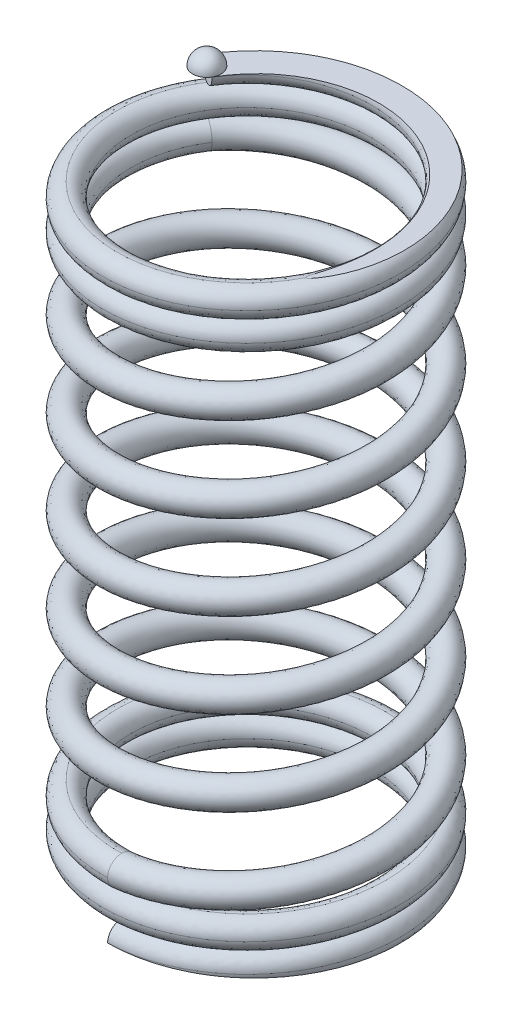
SolidWorks part; units mm, degrees
ref_plane "Front Plane" through (0, 0, 0) normal (0, 0, 1) x (1, 0, 0)
ref_plane "Top Plane" through (0, 0, 0) normal (0, 1, 0) x (1, 0, 0)
ref_plane "Right Plane" through (0, 0, 0) normal (1, 0, 0) x (0, 0, -1)
sketch "Sketch3" plane through (0, 0, 0) normal (0, 1, 0) x (1, 0, 0)
  circle A0 centre (0, 0) radius 4.75
  dimension "D1" = 9.5
ref_plane "Plane1" through (0, 2, 0) normal (0, 1, 0) x (1, 0, 0)
sketch "Sketch4" plane through (0, 0, 0) normal (0, 1, 0) x (1, 0, 0)
  circle A0 centre (0, 0) radius 4.75
  dimension "D1" = 9.5
curve "Helix/Spiral3" pitch 1 height 2 turns 2
sketch "Sketch5" plane through (0, 2, 0) normal (0, 1, 0) x (1, 0, 0)
  circle A0 centre (0, 0) radius 4.75
  dimension "D1" = 9.5
sketch "Sketch7" plane through (0, 0, 0) normal (1, 0, 0) x (0, 0, -1)
  line L0 (5.6185, 0) -> (-5.6185, 0) construction
  circle A0 centre (-4.75, 0) radius 0.5
  dimension "D2" = 1
  dimension "D1" = 4.75
sweep "Sweep5" add profiles "Sketch7" path "Helix/Spiral3"
sketch "Sketch13" plane through (0, 2, 0) normal (0, 1, 0) x (1, 0, 0)
  circle A0 centre (0, 0) radius 4.75
  dimension "D1" = 9.5
curve "Helix/Spiral6" pitch 3 height 17 turns 5.6667
sketch "Sketch15" plane through (0, 0, 0) normal (1, 0, 0) x (0, 0, -1)
  line L0 (5.6185, 2) -> (-5.6185, 2) construction
  circle A0 centre (-4.75, 2) radius 0.5
  spline S0 degree 3 poles (-4.75, 2) (-4.75, 2.0626) (-4.499, 2.1891) (-3.4274, 2.3777) (-1.8264, 2.5667) (0.0567, 2.7556) (1.9311, 2.9444) (3.5072, 3.1333) (4.5415, 3.3222) (4.8742, 3.5111) (4.454, 3.7) (3.3458, 3.8889) (1.7207, 4.0778) (-0.1702, 4.2667) (-2.0347, 4.4556) (-3.585, 4.6444) (-4.5815, 4.8333) (-4.8702, 5.0222) (-4.4067, 5.2111) (-3.2624, 5.4) (-1.6141, 5.5889) (0.2835, 5.7778) (2.1373, 5.9667) (3.6609, 6.1556) (4.6191, 6.3444) (4.8636, 6.5333) (4.3569, 6.7222) (3.1772, 6.9111) (1.5066, 7.1) (-0.3967, 7.2889) (-2.2387, 7.4778) (-3.7349, 7.6667) (-4.6541, 7.8556) (-4.8544, 8.0444) (-4.3048, 8.2333) (-3.0903, 8.4222) (-1.3983, 8.6111) (0.5096, 8.8) (2.3389, 8.9889) (3.8068, 9.1778) (4.6867, 9.3667) (4.8426, 9.5556) (4.2504, 9.7444) (3.0017, 9.9333) (1.2893, 10.1222) (-0.6223, 10.3111) (-2.4378, 10.5) (-3.8766, 10.6889) (-4.7167, 10.8778) (-4.8281, 11.0667) (-4.1937, 11.2556) (-2.9115, 11.4444) (-1.1795, 11.6333) (0.7347, 11.8222) (2.5354, 12.0111) (3.9444, 12.2) (4.7441, 12.3889) (4.811, 12.5778) (4.1347, 12.7667) (2.8197, 12.9556) (1.0691, 13.1444) (-0.8466, 13.3333) (-2.6316, 13.5222) (-4.01, 13.7111) (-4.769, 13.9) (-4.7913, 14.0889) (-4.0734, 14.2778) (-2.7264, 14.4667) (-0.9581, 14.6556) (0.9581, 14.8444) (2.7264, 15.0333) (4.0734, 15.2222) (4.7913, 15.4111) (4.769, 15.6) (4.01, 15.7889) (2.6316, 15.9778) (0.8466, 16.1667) (-1.0691, 16.3556) (-2.8197, 16.5444) (-4.1347, 16.7333) (-4.811, 16.9222) (-4.7441, 17.1111) (-3.9444, 17.3) (-2.5354, 17.4889) (-0.7347, 17.6778) (1.1795, 17.8667) (2.9115, 18.0556) (4.1936, 18.2444) (4.8282, 18.4333) (4.7162, 18.6223) (3.8782, 18.8109) (2.914, 18.9374) (2.375, 19) knots 0 0 0 0 0.011111 0.022222 0.033333 0.044444 0.055556 0.066667 0.077778 0.088889 0.1 0.111111 0.122222 0.133333 0.144444 0.155556 0.166667 0.177778 0.188889 0.2 0.211111 0.222222 0.233333 0.244444 0.255556 0.266667 0.277778 0.288889 0.3 0.311111 0.322222 0.333333 0.344444 0.355556 0.366667 0.377778 0.388889 0.4 0.411111 0.422222 0.433333 0.444444 0.455556 0.466667 0.477778 0.488889 0.5 0.511111 0.522222 0.533333 0.544444 0.555556 0.566667 0.577778 0.588889 0.6 0.611111 0.622222 0.633333 0.644444 0.655556 0.666667 0.677778 0.688889 0.7 0.711111 0.722222 0.733333 0.744444 0.755556 0.766667 0.777778 0.788889 0.8 0.811111 0.822222 0.833333 0.844444 0.855556 0.866667 0.877778 0.888889 0.9 0.911111 0.922222 0.933333 0.944444 0.955556 0.966667 0.977778 0.988889 1 1 1 1 construction
sweep "Sweep6" add profiles "Sketch15" path "Helix/Spiral6"
ref_plane "Plane4" through (0, 19, 0) normal (0, 1, 0) x (1, 0, 0)
sketch "Sketch16" plane through (0, 19, 0) normal (0, 1, 0) x (1, 0, 0)
  circle A0 centre (0, 0) radius 4.75
  dimension "D1" = 9.5
curve "Helix/Spiral7" pitch 1 height 2 turns 2
sketch "Sketch18" plane through (0, 0, 0) normal (-1, 0, 0) x (0, 0, 1)
  line L0 (5.6185, 0) -> (-5.6185, 0) construction
  line L1 (6.9903, 0) -> (-6.0243, 0)
  line L2 (6.9903, 0) -> (6.9903, -2.7149)
  line L3 (6.9903, -2.7149) -> (-6.0243, -2.7149)
  line L4 (-6.0243, 0) -> (-6.0243, -2.7149)
extrude "Cut-Extrude1" cut sketch "Sketch18" against normal mid plane 15
sketch "Sketch26" plane through (0, 19, 0) normal (0, 1, 0) x (1, 0, 0)
  circle A0 centre (0, 0) radius 4.75
  dimension "D1" = 9.5
curve "Helix/Spiral8" pitch 1 height 2 turns 2
sketch "Sketch27" plane through (0, 0, 0) normal (-0.5, 0, 0.866) x (0.866, 0, 0.5)
  circle A0 centre (-4.75, 19.0007) radius 0.5
sweep "Sweep7" add profiles "Sketch27" path "Helix/Spiral8"
sketch "Sketch28" plane through (0, 0, 0) normal (-0.5, 0, 0.866) x (0.866, 0, 0.5)
  line L0 (-5.3532, 21.0007) -> (-3.9959, 21.0007)
  line L1 (-3.9959, 21.0007) -> (7.3096, 21.0007)
  line L2 (7.3096, 21.0007) -> (7.3096, 23.8406)
  line L3 (7.3096, 23.8406) -> (-5.3532, 23.8406)
  line L4 (-5.3532, 23.8406) -> (-5.3532, 21.0007)
extrude "Cut-Extrude2" cut sketch "Sketch28" against normal mid plane 15
sketch "Sketch29" plane through (0, 0, 0) normal (-0.5, 0, 0.866) x (0.866, 0, 0.5)
  line L0 (-4.75, 21.7557) -> (-4.75, 19.8257) construction
  line L1 (-5.25, 21.0007) -> (-4.25, 21.0007) construction
  line L2 (-5.25, 21.0007) -> (-4.75, 21.0007)
  line L3 (-4.75, 21.0007) -> (-4.75, 21.5007)
  arc A0 (-4.75, 21.5007) -> (-5.25, 21.0007) centre (-4.75, 21.0007) ccw
revolve "Revolve1" add sketch "Sketch29" angle 360 about L0
sketch "Sketch30" plane through (0, 0, 0) normal (0, 0, 1) x (1, 0, 0)
  line L0 (0, 29.6261) -> (0, -9.9494) construction
sketch "Sketch31" plane through (0, 0, 0) normal (0, 0, 1) x (1, 0, 0)
  line L0 (0, 28.5085) -> (0, -6.6455) construction
